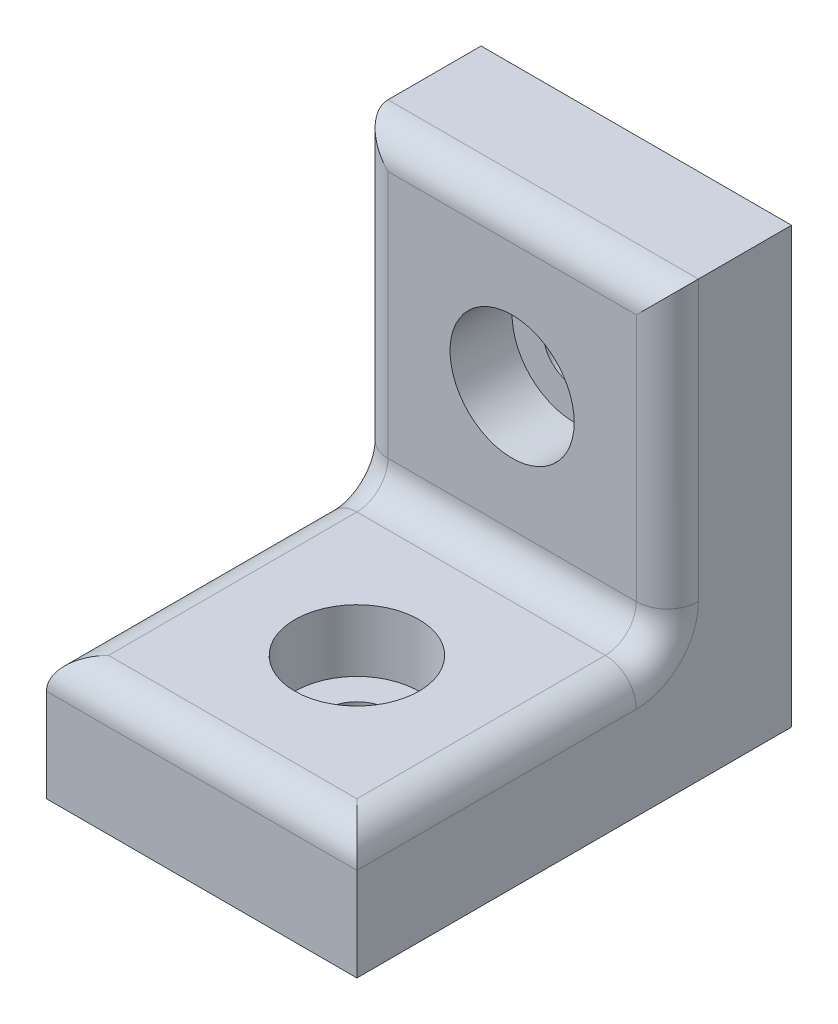
SolidWorks part; units mm, degrees
ref_plane "Plan de face" through (0, 0, 0) normal (0, 0, 1) x (1, 0, 0)
ref_plane "Plan de dessus" through (0, 0, 0) normal (0, 1, 0) x (1, 0, 0)
ref_plane "Plan de droite" through (0, 0, 0) normal (1, 0, 0) x (0, 0, -1)
sketch "Esquisse1" plane through (0, 0, 0) normal (0, 0, 1) x (1, 0, 0)
  line L1 (-5, 14) -> (5, 14)
  line L2 (-5, 14) -> (-5, 0)
  line L3 (-5, 0) -> (5, 0)
  line L4 (5, 14) -> (5, 0)
  dimension "D1" = 10
  dimension "D2" = 14
  dimension "D3" = 5
extrude "Boss.-Extru.1" add sketch "Esquisse1" along normal blind 4
sketch "Esquisse2" plane through (0, 0, 4) normal (0, 0, 1) x (1, 0, 0)
  line L0 (5, 0) -> (5, 14) construction
  line L1 (-5, 0) -> (5, 0)
  line L2 (-5, 0) -> (-5, 4)
  line L3 (-5, 4) -> (5, 4)
  line L4 (5, 0) -> (5, 4)
  dimension "D1" = 4
extrude "Boss.-Extru.2" add sketch "Esquisse2" along normal blind 10
sketch "Esquisse3" plane through (0, 0, 4) normal (0, 0, 1) x (1, 0, 0)
  line L0 (5, 14) -> (-5, 14) construction
  line L1 (-5, 14) -> (-5, 4) construction
  circle A0 centre (0, 9) radius 1
  point P2 (0, 14)
  point P3 (-5, 9)
  dimension "D1" = 2
extrude "Enlèv. mat.-Extru.1" cut sketch "Esquisse3" against normal through all
fillet "Congé1" radius 1 7 edges at (0, 4, 4) (5, 9, 4) (-5, 9, 4) (0, 4, 14) (5, 4, 9) (-5, 4, 9) (0, 14, 4)
sketch "Esquisse4" plane through (0, 4, 0) normal (0, 1, 0) x (1, 0, 0)
  line L0 (5, -14) -> (-5, -14) construction
  line L1 (-5, -14) -> (-5, -4) construction
  circle A0 centre (0, -9) radius 1
  point P0 (0, -14)
  point P1 (-5, -9)
  dimension "D1" = 2
extrude "Enlèv. mat.-Extru.2" cut sketch "Esquisse4" against normal through all
sketch "Esquisse5" plane through (0, 0, 4) normal (0, 0, 1) x (1, 0, 0)
  circle A0 centre (0, 9) radius 2
  dimension "D1" = 4
extrude "Enlèv. mat.-Extru.3" cut sketch "Esquisse5" against normal blind 2
sketch "Esquisse6" plane through (0, 4, 0) normal (0, 1, 0) x (1, 0, 0)
  circle A0 centre (0, -9) radius 2
  dimension "D1" = 4
extrude "Enlèv. mat.-Extru.4" cut sketch "Esquisse6" against normal blind 2
